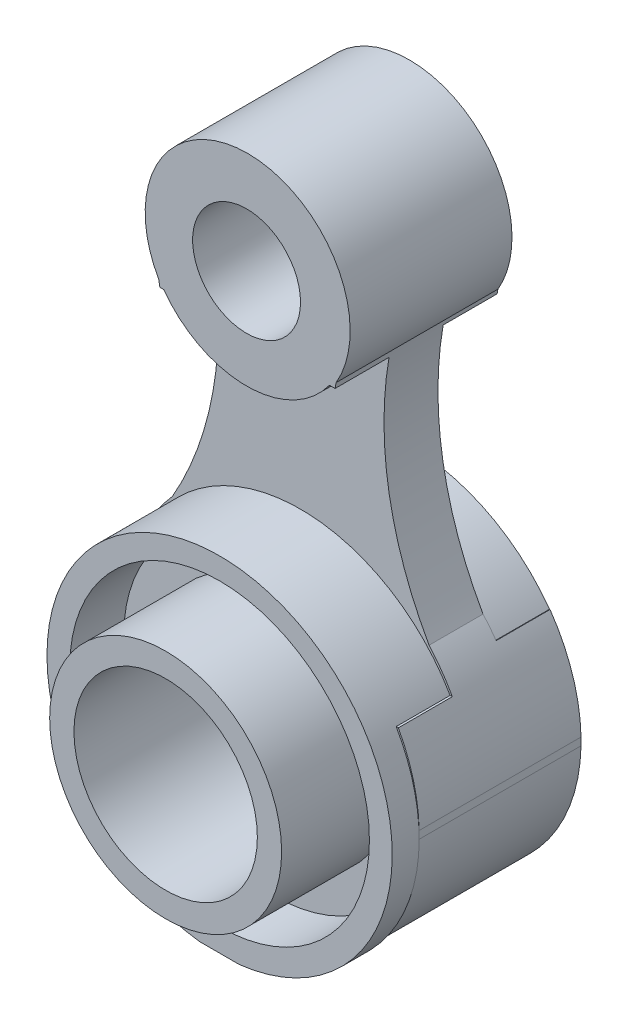
SolidWorks part; units mm, degrees
material "Alliage 1060"
ref_plane "Plan de face" through (0, 0, 0) normal (0, 0, 1) x (1, 0, 0)
ref_plane "Plan de dessus" through (0, 0, 0) normal (0, 1, 0) x (1, 0, 0)
ref_plane "Plan de droite" through (0, 0, 0) normal (1, 0, 0) x (0, 0, -1)
sketch "Esquisse1" plane through (0, 0, 0) normal (0, 0, 1) x (1, 0, 0)
  line L1 (-32, 63) -> (32, 63)
  line L2 (-32, 63) -> (-32, -63)
  line L3 (-32, -63) -> (32, -63)
  line L4 (32, 63) -> (32, -63)
extrude "Boss.-Extru.1" add sketch "Esquisse1" along normal blind 45
sketch "Esquisse2" plane through (0, 0, 45) normal (0, 0, 1) x (1, 0, 0)
  line L2 (-37.8967, -75.0543) -> (36.863, -75.0543)
  line L3 (-37.8967, -75.0543) -> (-37.8967, 64.3281)
  line L4 (-37.8967, 64.3281) -> (36.863, 64.3281)
  line L5 (36.863, -75.0543) -> (36.863, 64.3281)
  line L6 (32, -63) -> (32, 63) construction
  circle A0 centre (0, -31.2122) radius 32
  dimension "D1" = 32
extrude "Enlèv. mat.-Extru.2" cut sketch "Esquisse2" against normal blind 15
sketch "Esquisse3" plane through (0, 0, 45) normal (0, 0, 1) x (1, 0, 0)
  line L1 (-38.0327, 10.9827) -> (44.1343, 10.9827)
  line L2 (-38.0327, 10.9827) -> (-38.0327, -69.7606)
  line L3 (-38.0327, -69.7606) -> (44.1343, -69.7606)
  line L4 (44.1343, 10.9827) -> (44.1343, -69.7606)
  circle A0 centre (0, -31.2122) radius 27.5
  circle A1 centre (0, -31.2122) radius 21.5
extrude "Enlèv. mat.-Extru.5" cut sketch "Esquisse3" against normal blind 10 contours A1 A0
sketch "Esquisse5" plane through (0, 0, 45) normal (0, 0, 1) x (1, 0, 0)
  circle A0 centre (0, -31) radius 21.5
  circle A1 centre (0, -31) radius 27.775
extrude "Enlèv. mat.-Extru.7" cut sketch "Esquisse5" against normal blind 20
sketch "Esquisse6" plane through (0, 0, 45) normal (0, 0, 1) x (1, 0, 0)
  circle A0 centre (0, -30.9143) radius 17
extrude "Enlèv. mat.-Extru.8" cut sketch "Esquisse6" against normal through all
sketch "Esquisse7" plane through (0, 0, 30) normal (0, 0, 1) x (1, 0, 0)
  circle A0 centre (0, 44) radius 10
extrude "Enlèv. mat.-Extru.9" cut sketch "Esquisse7" against normal through all
sketch "Esquisse8" plane through (0, 0, 30) normal (0, 0, 1) x (1, 0, 0)
  line L3 (-44.6631, 65.4082) -> (41.7343, 65.4082)
  line L4 (-44.6631, 65.4082) -> (-44.6631, -71.0216)
  line L5 (-44.6631, -71.0216) -> (41.7343, -71.0216)
  line L6 (41.7343, 65.4082) -> (41.7343, -71.0216)
  circle A0 centre (0.2022, 44) radius 19
  arc A1 (-18.7978, 44) -> (-25.394, -11.7406) centre (-79.2158, 22.8891) cw
  arc A2 (32, -31.2122) -> (-32, -31.2122) centre (0, -31.2122) ccw construction
  arc A5 (25.394, -11.7406) -> (19.2022, 44) centre (79.4761, 22.4812) cw
  arc A6 (3.6791, -63) -> (-3.6791, -63) centre (0, -31.2122) ccw construction
  circle A7 centre (0, -30.5076) radius 32.0078
  line M4 (32, -31.2122) -> (32, 63)
  line M5 (32, 63) -> (-32, 63)
  line M6 (-32, 63) -> (-32, -31.2122)
extrude "Enlèv. mat.-Extru.11" cut sketch "Esquisse8" against normal through all contours A7 A1 A0 M5 M6 | A7 A0 A5 M4 M5 | L6 L3 L4 L5 A7 M6 M5 M4
sketch "Esquisse10" plane through (0, 0, 30) normal (0, 0, 1) x (1, 0, 0)
  line L1 (-31.1177, 33.3549) -> (30.3042, 33.3549)
  line L2 (-31.1177, 33.3549) -> (-31.1177, -15.2538)
  line L3 (-31.1177, -15.2538) -> (30.3042, -15.2538)
  line L4 (30.3042, 33.3549) -> (30.3042, -15.2538)
  circle A0 centre (0, 44.541) radius 19
  circle A1 centre (0, -31.2122) radius 32
  arc M3 (-23.7637, -9.065) -> (-32, -29.8029) centre (0, -30.5076) ccw
  arc M5 (-32, -31.2122) -> (32, -31.2122) centre (0, -31.2122) cw
  arc M7 (32, -29.8029) -> (23.8375, -9.147) centre (0, -30.5076) ccw
  arc M8 (23.8375, -9.147) -> (16.5943, 34.3929) centre (79.4761, 22.4812) cw
  arc M10 (-16.2899, 34.5655) -> (-23.7637, -9.065) centre (-79.2158, 22.8891) cw
extrude "Enlèv. mat.-Extru.12" cut sketch "Esquisse10" against normal blind 10 contours A0 L1 L3 M10 M3 M5 M7 M8
sketch "Esquisse11" plane through (0, 0, 0) normal (0, 0, -1) x (-1, 0, 0)
  line L5 (-31.3211, 33.5583) -> (28.8805, 33.5583)
  line L6 (-31.3211, 33.5583) -> (-31.3211, -12.203)
  line L7 (-31.3211, -12.203) -> (28.8805, -12.203)
  line L8 (28.8805, 33.5583) -> (28.8805, -12.203)
  circle A0 centre (0, 44.541) radius 19
  circle A1 centre (-0.2034, -30.9143) radius 0.2876
  circle A2 centre (-0.2034, -30.9143) radius 32
  arc M8 (32, -29.8029) -> (23.7637, -9.065) centre (0, -30.5076) ccw
  arc M9 (23.7637, -9.065) -> (16.2899, 34.5655) centre (79.2158, 22.8891) cw
  arc M11 (-16.5943, 34.3929) -> (-23.8375, -9.147) centre (-79.4761, 22.4812) cw
  arc M12 (-23.8375, -9.147) -> (-32, -29.8029) centre (0, -30.5076) ccw
extrude "Enlèv. mat.-Extru.13" cut sketch "Esquisse11" against normal blind 10 contours A2 L7 L5 A0 M8 M9 M11 M12
